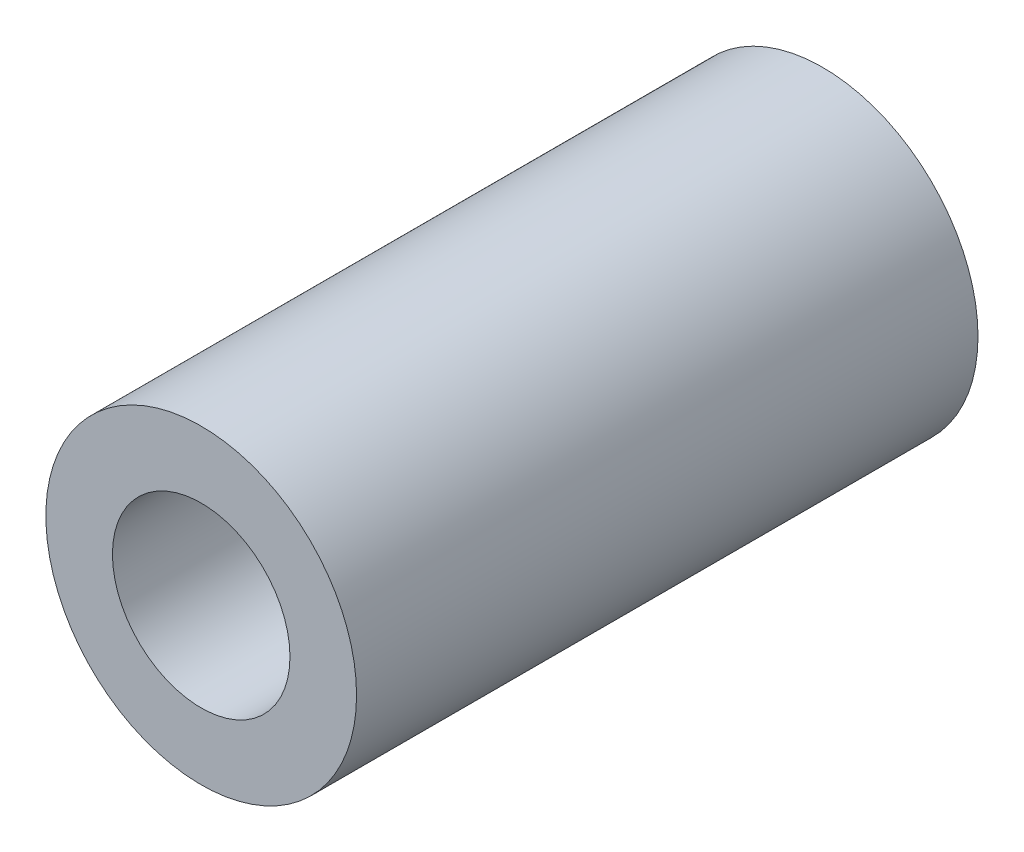
SolidWorks part; units mm, degrees
material "Brass"
ref_plane "Front" through (0, 0, 0) normal (0, 0, 1) x (1, 0, 0)
ref_plane "Top" through (0, 0, 0) normal (0, 1, 0) x (1, 0, 0)
ref_plane "Right" through (0, 0, 0) normal (1, 0, 0) x (0, 0, -1)
sketch "Sketch1" plane through (0, 0, 0) normal (0, 0, 1) x (1, 0, 0)
  circle A0 centre (0, 0) radius 7
  dimension "D1" = 14
extrude "Boss-Extrude2" add sketch "Sketch1" against normal blind 28
sketch "Sketch2" plane through (0, 0, 0) normal (0, 0, 1) x (1, 0, 0)
  circle A0 centre (0, 0) radius 4
  dimension "D1" = 8
extrude "Cut-Extrude1" cut sketch "Sketch2" against normal through all
